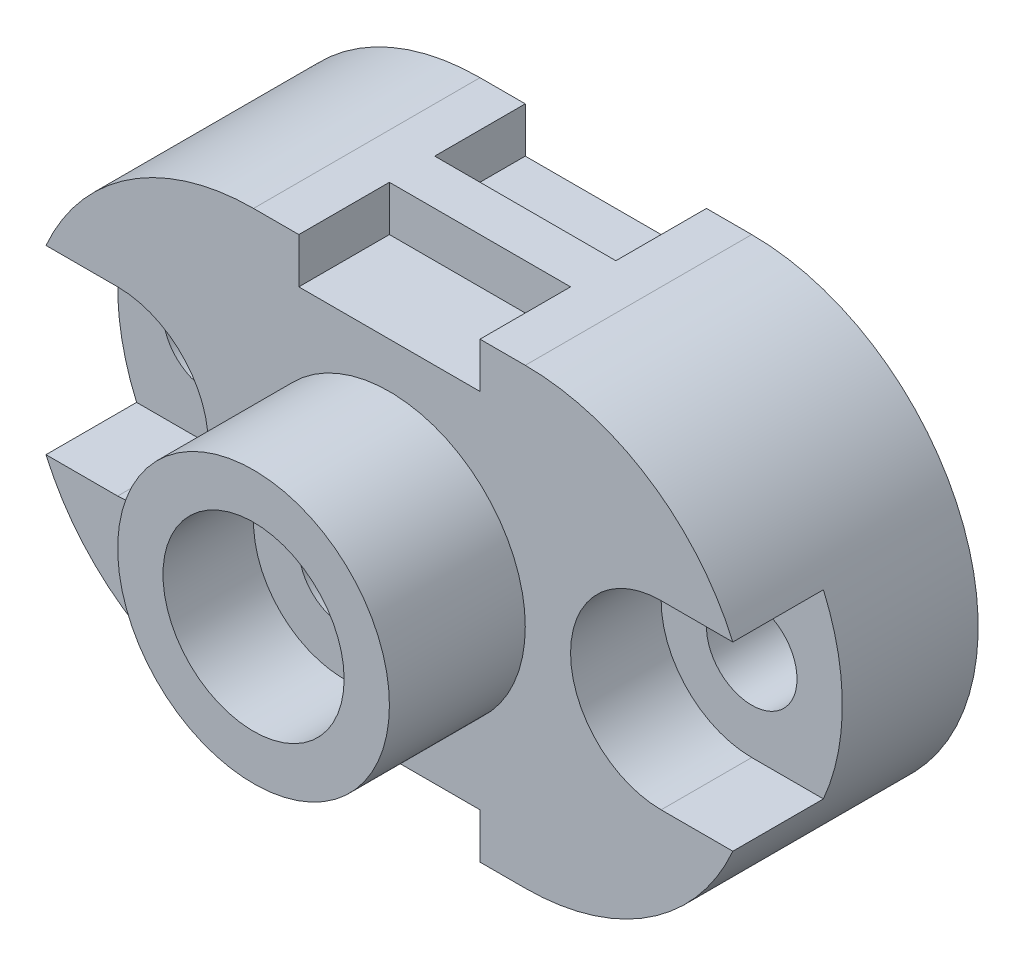
SolidWorks part; units mm, degrees
ref_plane "Front Plane" through (0, 0, 0) normal (0, 0, 1) x (1, 0, 0)
ref_plane "Top Plane" through (0, 0, 0) normal (0, 1, 0) x (1, 0, 0)
ref_plane "Right Plane" through (0, 0, 0) normal (1, 0, 0) x (0, 0, -1)
sketch "Sketch1" plane through (0, 0, 0) normal (0, 0, 1) x (1, 0, 0)
  line L0 (0, 50) -> (60, 50)
  line L1 (0, -50) -> (60, -50)
  arc A0 (0, 50) -> (0, -50) centre (0, 0) ccw
  arc A1 (60, 50) -> (60, -50) centre (60, 0) cw
  dimension "D1" = 50
  dimension "D2" = 50
  dimension "D3" = 60
  dimension "D4" = 60
extrude "Boss-Extrude1" add sketch "Sketch1" along normal blind 50
sketch "Sketch2" plane through (0, 0, 50) normal (0, 0, 1) x (1, 0, 0)
  circle A0 centre (30, 0) radius 10
  dimension "D1" = 20
  dimension "D2" = 30
  dimension "D3" = 50
extrude "Cut-Extrude1" cut sketch "Sketch2" against normal blind 50
sketch "Sketch3" plane through (0, 0, 50) normal (0, 0, 1) x (1, 0, 0)
  circle A0 centre (30, 0) radius 30
  dimension "D1" = 60
extrude "Boss-Extrude2" add sketch "Sketch3" along normal blind 30
sketch "Sketch4" plane through (0, 0, 80) normal (0, 0, 1) x (1, 0, 0)
  circle A0 centre (30, 0) radius 20
  dimension "D1" = 40
extrude "Cut-Extrude2" cut sketch "Sketch4" against normal blind 20
sketch "Sketch5" plane through (0, 0, 50) normal (0, 0, -1) x (-1, 0, 0)
  circle A0 centre (-30, 0) radius 10
  dimension "D1" = 20
extrude "Cut-Extrude3" cut sketch "Sketch5" against normal blind 20
sketch "Sketch6" plane through (0, 0, 50) normal (0, 0, 1) x (1, 0, 0)
  line L0 (60, 50) -> (0, 50) construction
  line L1 (50, 50) -> (10, 50)
  line L2 (50, 50) -> (50, 40)
  line L3 (50, 40) -> (10, 40)
  line L4 (10, 50) -> (10, 40)
  dimension "D1" = 40
  dimension "D2" = 10
  dimension "D3" = 10
extrude "Cut-Extrude4" cut sketch "Sketch6" against normal blind 20
sketch "Sketch7" plane through (0, 0, 0) normal (0, 0, -1) x (-1, 0, 0)
  line L0 (-60, 50) -> (0, 50) construction
  line L1 (-10, 50) -> (-50, 50)
  line L2 (-10, 50) -> (-10, 40)
  line L3 (-10, 40) -> (-50, 40)
  line L4 (-50, 50) -> (-50, 40)
  dimension "D1" = 40
  dimension "D2" = 10
  dimension "D3" = 10
extrude "Cut-Extrude5" cut sketch "Sketch7" against normal blind 20
sketch "Sketch8" plane through (0, 0, 50) normal (0, 0, 1) x (1, 0, 0)
  line L0 (0, -50) -> (60, -50) construction
  line L1 (50, -50) -> (10, -50)
  line L2 (50, -50) -> (50, -40)
  line L3 (50, -40) -> (10, -40)
  line L4 (10, -50) -> (10, -40)
  dimension "D1" = 40
  dimension "D2" = 10
  dimension "D3" = 10
extrude "Cut-Extrude6" cut sketch "Sketch8" against normal blind 20
sketch "Sketch9" plane through (0, 0, 0) normal (0, 0, -1) x (-1, 0, 0)
  line L0 (0, -50) -> (-60, -50) construction
  line L1 (-10, -50) -> (-50, -50)
  line L2 (-10, -50) -> (-10, -40)
  line L3 (-10, -40) -> (-50, -40)
  line L4 (-50, -50) -> (-50, -40)
  dimension "D1" = 40
  dimension "D2" = 10
  dimension "D3" = 10
extrude "Cut-Extrude7" cut sketch "Sketch9" against normal blind 20
sketch "Sketch10" plane through (0, 0, 50) normal (0, 0, 1) x (1, 0, 0)
  circle A0 centre (-30, 0) radius 10
  circle A1 centre (90, 0) radius 10
  circle A2 centre (30, 0) radius 10 construction
  circle A3 centre (30, 0) radius 10 construction
  dimension "D1" = 20
  dimension "D2" = 20
  dimension "D3" = 60
  dimension "D4" = 60
  dimension "D5" = 30
extrude "Cut-Extrude8" cut sketch "Sketch10" against normal blind 60
sketch "Sketch11" plane through (0, 0, 50) normal (0, 0, 1) x (1, 0, 0)
  line L0 (-30, 20) -> (-45.8258, 20)
  line L1 (-30, -20) -> (-45.8258, -20)
  line L2 (90, 20) -> (105.8258, 20)
  line L3 (90, -20) -> (105.8258, -20)
  line L4 (-30, 20) -> (-45.8258, 20)
  arc A0 (-30, 20) -> (-30, -20) centre (-30, 0) cw
  arc A1 (90, 20) -> (90, -20) centre (90, 0) ccw
  arc A2 (0, 50) -> (0, -50) centre (0, 0) ccw construction
  arc A3 (60, -50) -> (60, 50) centre (60, 0) ccw construction
  arc A4 (60, 50) -> (105.8258, -20) centre (60, 0) cw
  circle A5 centre (30, 0) radius 30 construction
  circle M1 centre (90, 0) radius 10
  circle M2 centre (-30, 0) radius 10
  arc M5 (60, -50) -> (60, 50) centre (60, 0) ccw
  arc M11 (0, 50) -> (0, -50) centre (0, 0) ccw
  dimension "D3" = 50
  dimension "D1" = 20
  dimension "D2" = 20
extrude "Cut-Extrude9" cut sketch "Sketch11" against normal blind 20 contours A0 L0 L1 M11 M2 | L2 A1 L3 M5 M1
